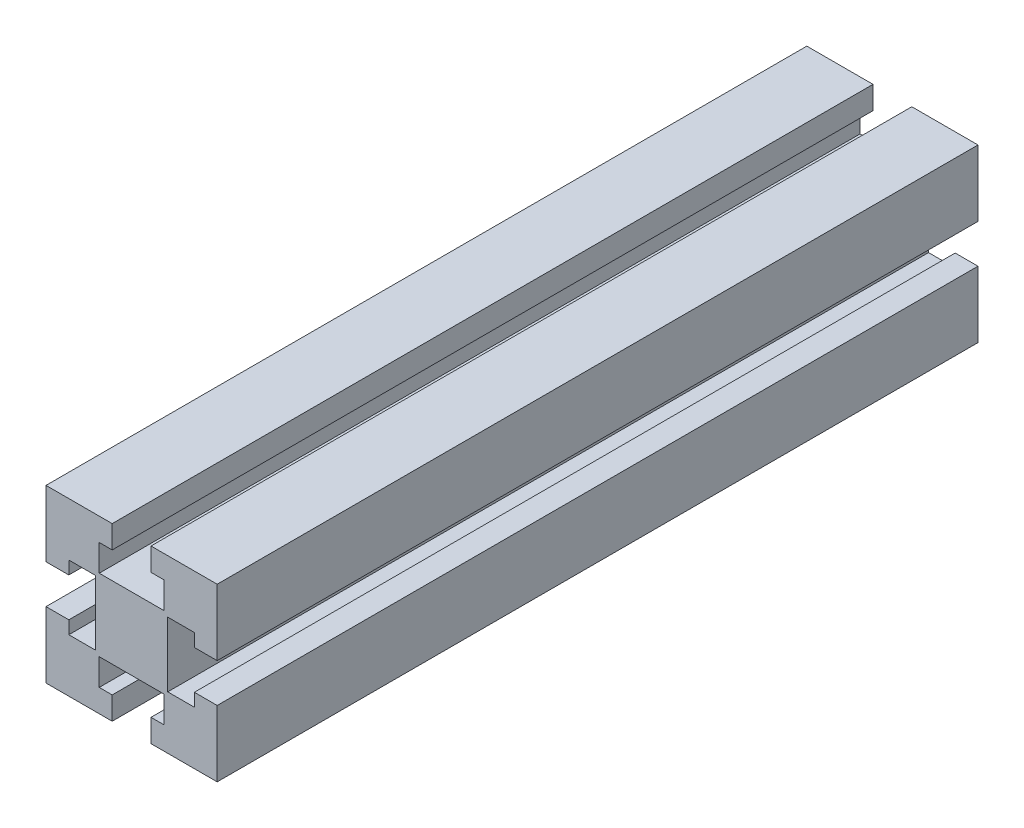
SolidWorks part; units mm, degrees
ref_plane "Ebene vorne" through (0, 0, 0) normal (0, 0, 1) x (1, 0, 0)
ref_plane "Ebene oben" through (0, 0, 0) normal (0, 1, 0) x (1, 0, 0)
ref_plane "Ebene rechts" through (0, 0, 0) normal (1, 0, 0) x (0, 0, -1)
sketch "Skizze1" plane through (0, 0, 0) normal (0, 0, 1) x (1, 0, 0)
  line L39 (-18.8192, 33.7768) -> (-1.4192, 33.7768)
  line L43 (-46.4192, 33.7768) -> (-29.0192, 33.7768)
  line L44 (-46.4192, 33.7768) -> (-46.4192, 16.3768)
  line L45 (-46.4192, -11.2232) -> (-29.0192, -11.2232)
  line L46 (-1.4192, 33.7768) -> (-1.4192, 16.3768)
  line L47 (-32.4242, 27.7768) -> (-29.0192, 27.7768)
  line L48 (-32.4242, 27.7768) -> (-32.4242, 20.7768)
  line L49 (-32.4242, 20.7768) -> (-15.4143, 20.7768)
  line L50 (-15.4143, 27.7768) -> (-15.4143, 20.7768)
  line L51 (-14.4192, 19.7817) -> (-7.4192, 19.7817)
  line L52 (-14.4192, 19.7817) -> (-14.4192, 2.7718)
  line L53 (-14.4192, 2.7718) -> (-7.4192, 2.7718)
  line L54 (-7.4192, 19.7817) -> (-7.4192, 16.3768)
  line L55 (-32.4242, 1.7768) -> (-15.4143, 1.7768)
  line L56 (-32.4242, 1.7768) -> (-32.4242, -5.2232)
  line L57 (-32.4242, -5.2232) -> (-29.0192, -5.2232)
  line L58 (-15.4143, 1.7768) -> (-15.4143, -5.2232)
  line L59 (-40.4192, 19.7817) -> (-33.4192, 19.7817)
  line L60 (-40.4192, 19.7817) -> (-40.4192, 16.3768)
  line L61 (-40.4192, 2.7718) -> (-33.4192, 2.7718)
  line L62 (-33.4192, 19.7817) -> (-33.4192, 2.7718)
  line L64 (-29.0192, 27.7768) -> (-29.0192, 33.7768)
  line L66 (-18.8192, 27.7768) -> (-18.8192, 33.7768)
  line L67 (-7.4192, 16.3768) -> (-1.4192, 16.3768)
  line L69 (-7.4192, 6.1768) -> (-1.4192, 6.1768)
  line L72 (-29.0192, -5.2232) -> (-29.0192, -11.2232)
  line L74 (-18.8192, -5.2232) -> (-18.8192, -11.2232)
  line L75 (-40.4192, 16.3768) -> (-46.4192, 16.3768)
  line L77 (-40.4192, 6.1768) -> (-46.4192, 6.1768)
  line L79 (-18.8192, 27.7768) -> (-15.4143, 27.7768)
  line L80 (-7.4192, 6.1768) -> (-7.4192, 2.7718)
  line L81 (-1.4192, 6.1768) -> (-1.4192, -11.2232)
  line L82 (-18.8192, -11.2232) -> (-1.4192, -11.2232)
  line L83 (-18.8192, -5.2232) -> (-15.4143, -5.2232)
  line L84 (-46.4192, 6.1768) -> (-46.4192, -11.2232)
  line L85 (-40.4192, 6.1768) -> (-40.4192, 2.7718)
  dimension "D6" = 13
  dimension "D4" = 13
  dimension "D1" = 10.2
  dimension "D2" = 45
  dimension "D3" = 45
  dimension "D5" = 13
  dimension "D7" = 13
  dimension "D8" = 6
  dimension "D9" = 13.995
extrude "Aufsatz-Linear austragen1" add sketch "Skizze1" along normal blind 200 contours L43 L64 L47 L48 L49 L50 L79 L66 L39 L46 L67 L54 L51 L52 L53 L80 L69 L81 L82 L74 L83 L58 L55 L56 L57 L72 L45 L84 L77 L85 L61 L62 L59 L60 L75 L44
